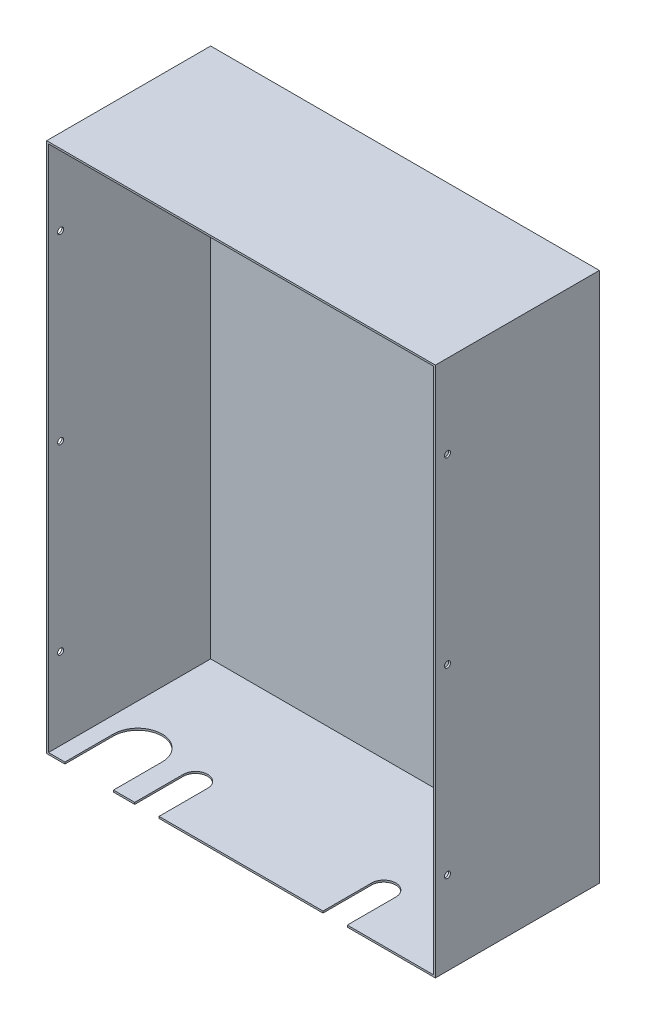
SolidWorks part; units mm, degrees
ref_plane "Alzado" through (0, 0, 0) normal (0, 0, 1) x (1, 0, 0)
ref_plane "Planta" through (0, 0, 0) normal (0, 1, 0) x (1, 0, 0)
ref_plane "Vista lateral" through (0, 0, 0) normal (1, 0, 0) x (0, 0, -1)
sketch "Croquis1" plane through (0, 0, 0) normal (0, 0, 1) x (1, 0, 0)
  line L1 (0, 0) -> (-320, 0)
  line L2 (0, 0) -> (0, 437)
  line L3 (0, 437) -> (-320, 437)
  line L4 (-320, 0) -> (-320, 437)
  dimension "D1" = 437
  dimension "D2" = 320
extrude "Saliente-Extruir1" add sketch "Croquis1" along normal blind 1.5 contours L2 L1 L4 L3
sketch "Croquis2" plane through (0, 0, 0) normal (0, 0, 1) x (1, 0, 0)
  line L0 (-320, 0) -> (-320, 437) construction
  line L1 (0, 437) -> (-320, 437)
  line L2 (0, 437) -> (0, 436)
  line L3 (-1.5, 435.5) -> (-318.5, 435.5)
  line L4 (-320, 437) -> (-320, 436)
  line L5 (0, 0) -> (-320, 0) construction
  line L6 (-320, 437) -> (-319, 437)
  line L7 (-320, 437) -> (-320, 0)
  line L8 (-320, 0) -> (-319, 0)
  line L9 (-318.5, 435.5) -> (-318.5, 1.5)
  line L10 (0, 0) -> (0, 437) construction
  line L11 (-320, 0) -> (0, 0)
  line L12 (-320, 0) -> (-320, 1)
  line L13 (-318.5, 1.5) -> (-1.5, 1.5)
  line L14 (0, 0) -> (0, 1)
  line L16 (0, 0) -> (-1, 0)
  line L17 (0, 0) -> (0, 437)
  line L18 (0, 437) -> (-1, 437)
  line L19 (-1.5, 1.5) -> (-1.5, 435.5)
  dimension "D1" = 1.5
  dimension "D2" = 1.5
  dimension "D3" = 1.5
  dimension "D4" = 1.5
extrude "Saliente-Extruir2" add sketch "Croquis2" along normal blind 135 contours L14 L17 L2 L1 L4 L7 L8 L11 L19 L13 L9 L3
sketch "Croquis3" plane through (0, 0, 0) normal (0, -1, 0) x (1, 0, 0)
  line L0 (-160, 0) -> (-160, 144.7443) construction
  line L1 (0, 0) -> (-320, 0) construction
  line L2 (-237.5, 95) -> (-82.5, 95) construction
  line L3 (-237.5, 95) -> (-237.5, 125.956) construction
  line L4 (-82.5, 95) -> (-82.5, 125.956) construction
  line L5 (-247.5, 95) -> (-247.5, 135)
  line L6 (-320, 135) -> (0, 135) construction
  line L7 (-227.5, 95) -> (-227.5, 135)
  line L8 (-92.5, 95) -> (-92.5, 135)
  line L9 (-72.5, 95) -> (-72.5, 135)
  line L10 (-247.5, 135) -> (-227.5, 135)
  line L11 (-72.5, 135) -> (-92.5, 135)
  arc A0 (-247.5, 95) -> (-227.5, 95) centre (-237.5, 95) ccw
  arc A1 (-92.5, 95) -> (-72.5, 95) centre (-82.5, 95) ccw
  point P6 (-160, 95)
  dimension "D2" = 20
  dimension "D3" = 20
  dimension "D1" = 155
  dimension "D4" = 40
extrude "Cortar-Extruir1" cut sketch "Croquis3" against normal up to surface (1.5 mm away) up to face at (-160, 1.5, 68.25)
sketch "Croquis4" plane through (0, 0, 0) normal (0, -1, 0) x (1, 0, 0)
  line L0 (-285, 143.2099) -> (-285, -20.422) construction
  line L1 (-320, 135) -> (-320, 0) construction
  line L2 (-320, 135) -> (-247.5, 135) construction
  line L3 (-305, 95) -> (-305, 135)
  line L4 (-265, 95) -> (-265, 135)
  line L15 (-227.5, 135) -> (-227.5, 95)
  line L16 (-247.5, 95) -> (-247.5, 135)
  line L17 (-247.5, 135) -> (-320, 135)
  line L18 (-320, 135) -> (-320, 0)
  line L19 (-320, 0) -> (0, 0)
  line L20 (0, 0) -> (0, 135)
  line L21 (0, 135) -> (-72.5, 135)
  line L22 (-72.5, 135) -> (-72.5, 95)
  line L23 (-92.5, 95) -> (-92.5, 135)
  line L24 (-92.5, 135) -> (-227.5, 135)
  line L27 (-265, 135) -> (-305, 135)
  arc A0 (-305, 95) -> (-265, 95) centre (-285, 95) ccw
  arc A3 (-247.5, 95) -> (-227.5, 95) centre (-237.5, 95) ccw
  arc A4 (-92.5, 95) -> (-72.5, 95) centre (-82.5, 95) ccw
  dimension "D2" = 40
  dimension "D1" = 35
  dimension "D3" = 40
  dimension "D4" = 0
extrude "Cortar-Extruir2" cut sketch "Croquis4" against normal up to surface (1.5 mm away) up to face at (-160, 1.5, 97.75)
sketch "Croquis6" plane through (-320, 0, 0) normal (-1, 0, 0) x (0, 0, 1)
  line L0 (135, 218.5) -> (-80.4516, 218.5) construction
  line L1 (135, 437) -> (135, 0) construction
  circle A0 centre (125, 368.5) radius 2.5
  circle A1 centre (125, 68.5) radius 2.5
  circle A2 centre (125, 218.5) radius 2.5
  dimension "D1" = 5
  dimension "D4" = 5
  dimension "D2" = 150
  dimension "D3" = 10
extrude "Cortar-Extruir4" cut sketch "Croquis6" against normal up to surface (320 mm away) up to face at (0, 218.5, 67.5)
